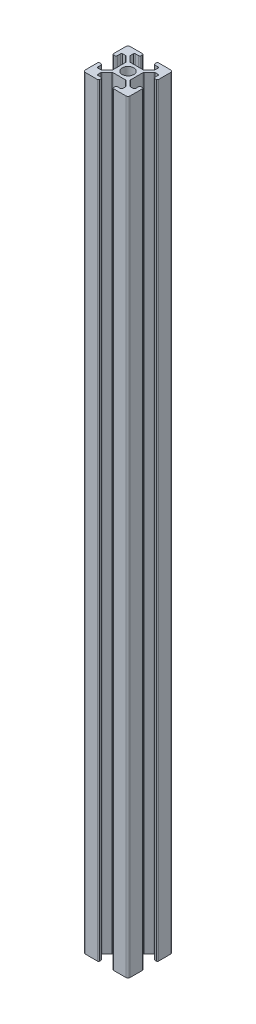
SolidWorks part; units mm, degrees
ref_plane "Front Plane" through (0, 0, 0) normal (0, 0, 1) x (1, 0, 0)
ref_plane "Top Plane" through (0, 0, 0) normal (0, 1, 0) x (1, 0, 0)
ref_plane "Right Plane" through (0, 0, 0) normal (1, 0, 0) x (0, 0, -1)
ref_plane "Plane1" through (0, 170, 0) normal (0, 1, 0) x (1, 0, 0)
sketch "Sketch1" plane through (0, 170, 0) normal (0, 1, 0) x (1, 0, 0)
  line L0 (-3.1, 8.85) -> (-3.1, 9.5)
  line L1 (-3.6, 10) -> (-9, 10)
  line L2 (-10, 9) -> (-10, 3.6)
  line L3 (-9.5, 3.1) -> (-8.85, 3.1)
  line L4 (-8.35, 3.6) -> (-8.35, 5)
  line L5 (-7.85, 5.5) -> (-6.6263, 5.5)
  line L6 (-6.2728, 5.3536) -> (-4.0464, 3.1272)
  line L7 (-3.9, 2.7737) -> (-3.9, -2.7737)
  line L8 (-4.0464, -3.1272) -> (-6.2728, -5.3536)
  line L9 (-6.6263, -5.5) -> (-7.85, -5.5)
  line L10 (-8.35, -5) -> (-8.35, -3.6)
  line L11 (-8.85, -3.1) -> (-9.5, -3.1)
  line L12 (-10, -3.6) -> (-10, -9)
  line L13 (-9, -10) -> (-3.6, -10)
  line L14 (-3.1, -9.5) -> (-3.1, -8.85)
  line L15 (-3.6, -8.35) -> (-5, -8.35)
  line L16 (-5.5, -7.85) -> (-5.5, -6.6263)
  line L17 (-5.3536, -6.2728) -> (-3.1272, -4.0464)
  line L18 (-2.7737, -3.9) -> (2.7737, -3.9)
  line L19 (3.1272, -4.0464) -> (5.3536, -6.2728)
  line L20 (5.5, -6.6263) -> (5.5, -7.85)
  line L21 (5, -8.35) -> (3.6, -8.35)
  line L22 (3.1, -8.85) -> (3.1, -9.5)
  line L23 (3.6, -10) -> (9, -10)
  line L24 (10, -9) -> (10, -3.6)
  line L25 (9.5, -3.1) -> (8.85, -3.1)
  line L26 (8.35, -3.6) -> (8.35, -5)
  line L27 (7.85, -5.5) -> (6.6263, -5.5)
  line L28 (6.2728, -5.3536) -> (4.0464, -3.1272)
  line L29 (3.9, -2.7737) -> (3.9, 2.7737)
  line L30 (4.0464, 3.1272) -> (6.2728, 5.3536)
  line L31 (6.6263, 5.5) -> (7.85, 5.5)
  line L32 (8.35, 5) -> (8.35, 3.6)
  line L33 (8.85, 3.1) -> (9.5, 3.1)
  line L34 (10, 3.6) -> (10, 9)
  line L35 (9, 10) -> (3.6, 10)
  line L36 (3.1, 9.5) -> (3.1, 8.85)
  line L37 (3.6, 8.35) -> (5, 8.35)
  line L38 (5.5, 7.85) -> (5.5, 6.6263)
  line L39 (5.3536, 6.2728) -> (3.1272, 4.0464)
  line L40 (2.7737, 3.9) -> (-2.7737, 3.9)
  line L41 (-3.1272, 4.0464) -> (-5.5, 6.4192)
  line L42 (-5.5, 6.4192) -> (-5.5, 7.85)
  line L43 (-5, 8.35) -> (-3.6, 8.35)
  circle A0 centre (0, 0) radius 2.6
  arc A1 (-3.1, 9.5) -> (-3.6, 10) centre (-3.6, 9.5) ccw
  arc A2 (-9, 10) -> (-10, 9) centre (-9, 9) ccw
  arc A3 (-10, 3.6) -> (-9.5, 3.1) centre (-9.5, 3.6) ccw
  arc A4 (-8.85, 3.1) -> (-8.35, 3.6) centre (-8.85, 3.6) ccw
  arc A5 (-8.35, 5) -> (-7.85, 5.5) centre (-7.85, 5) cw
  arc A6 (-6.6263, 5.5) -> (-6.2728, 5.3536) centre (-6.6263, 5) cw
  arc A7 (-4.0464, 3.1272) -> (-3.9, 2.7737) centre (-4.4, 2.7737) cw
  arc A8 (-3.9, -2.7737) -> (-4.0464, -3.1272) centre (-4.4, -2.7737) cw
  arc A9 (-6.2728, -5.3536) -> (-6.6263, -5.5) centre (-6.6263, -5) cw
  arc A10 (-7.85, -5.5) -> (-8.35, -5) centre (-7.85, -5) cw
  arc A11 (-8.35, -3.6) -> (-8.85, -3.1) centre (-8.85, -3.6) ccw
  arc A12 (-9.5, -3.1) -> (-10, -3.6) centre (-9.5, -3.6) ccw
  arc A13 (-10, -9) -> (-9, -10) centre (-9, -9) ccw
  arc A14 (-3.6, -10) -> (-3.1, -9.5) centre (-3.6, -9.5) ccw
  arc A15 (-3.1, -8.85) -> (-3.6, -8.35) centre (-3.6, -8.85) ccw
  arc A16 (-5, -8.35) -> (-5.5, -7.85) centre (-5, -7.85) cw
  arc A17 (-5.5, -6.6263) -> (-5.3536, -6.2728) centre (-5, -6.6263) cw
  arc A18 (-3.1272, -4.0464) -> (-2.7737, -3.9) centre (-2.7737, -4.4) cw
  arc A19 (2.7737, -3.9) -> (3.1272, -4.0464) centre (2.7737, -4.4) cw
  arc A20 (5.3536, -6.2728) -> (5.5, -6.6263) centre (5, -6.6263) cw
  arc A21 (5.5, -7.85) -> (5, -8.35) centre (5, -7.85) cw
  arc A22 (3.6, -8.35) -> (3.1, -8.85) centre (3.6, -8.85) ccw
  arc A23 (3.1, -9.5) -> (3.6, -10) centre (3.6, -9.5) ccw
  arc A24 (9, -10) -> (10, -9) centre (9, -9) ccw
  arc A25 (10, -3.6) -> (9.5, -3.1) centre (9.5, -3.6) ccw
  arc A26 (8.85, -3.1) -> (8.35, -3.6) centre (8.85, -3.6) ccw
  arc A27 (8.35, -5) -> (7.85, -5.5) centre (7.85, -5) cw
  arc A28 (6.6263, -5.5) -> (6.2728, -5.3536) centre (6.6263, -5) cw
  arc A29 (4.0464, -3.1272) -> (3.9, -2.7737) centre (4.4, -2.7737) cw
  arc A30 (3.9, 2.7737) -> (4.0464, 3.1272) centre (4.4, 2.7737) cw
  arc A31 (6.2728, 5.3536) -> (6.6263, 5.5) centre (6.6263, 5) cw
  arc A32 (7.85, 5.5) -> (8.35, 5) centre (7.85, 5) cw
  arc A33 (8.35, 3.6) -> (8.85, 3.1) centre (8.85, 3.6) ccw
  arc A34 (9.5, 3.1) -> (10, 3.6) centre (9.5, 3.6) ccw
  arc A35 (10, 9) -> (9, 10) centre (9, 9) ccw
  arc A36 (3.6, 10) -> (3.1, 9.5) centre (3.6, 9.5) ccw
  arc A37 (3.1, 8.85) -> (3.6, 8.35) centre (3.6, 8.85) ccw
  arc A38 (5, 8.35) -> (5.5, 7.85) centre (5, 7.85) cw
  arc A39 (5.5, 6.6263) -> (5.3536, 6.2728) centre (5, 6.6263) cw
  arc A40 (3.1272, 4.0464) -> (2.7737, 3.9) centre (2.7737, 4.4) cw
  arc A41 (-2.7737, 3.9) -> (-3.1272, 4.0464) centre (-2.7737, 4.4) cw
  arc A42 (-5.5, 7.85) -> (-5, 8.35) centre (-5, 7.85) cw
  arc A43 (-3.6, 8.35) -> (-3.1, 8.85) centre (-3.6, 8.85) ccw
extrude "Boss-Extrude1" add sketch "Sketch1" against normal blind 340
